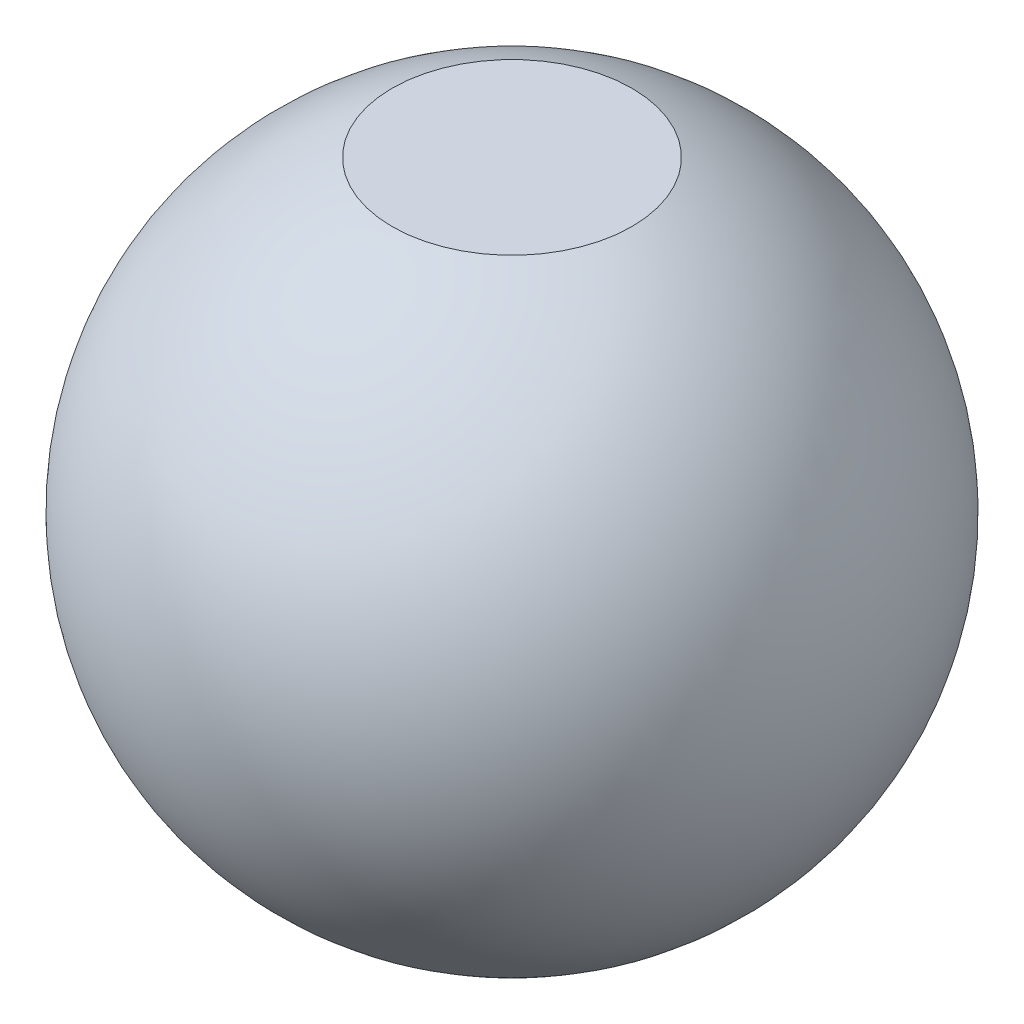
SolidWorks part; units mm, degrees
material "ABS PC"
ref_plane "Front Plane" through (0, 0, 0) normal (0, 0, 1) x (1, 0, 0)
ref_plane "Top Plane" through (0, 0, 0) normal (0, 1, 0) x (1, 0, 0)
ref_plane "Right Plane" through (0, 0, 0) normal (1, 0, 0) x (0, 0, -1)
sketch "Sketch1" plane through (0, 0, 0) normal (0, 0, 1) x (1, 0, 0)
  line L0 (0, -55) -> (0, 55) construction
  line L1 (19.9994, 51.235) -> (0, 51.235)
  line L2 (0, 51.235) -> (0, -51.235)
  line L3 (0, -51.235) -> (19.9994, -51.235)
  line L4 (55, 0) -> (-55, 0) construction
  arc A0 (19.9994, 51.235) -> (19.9994, -51.235) centre (0, 0) cw
  point P12 (0, 0)
  dimension "D1" = 55
  dimension "D2" = 102.47
revolve "Revolve1" add sketch "Sketch1" angle 360 about L2
